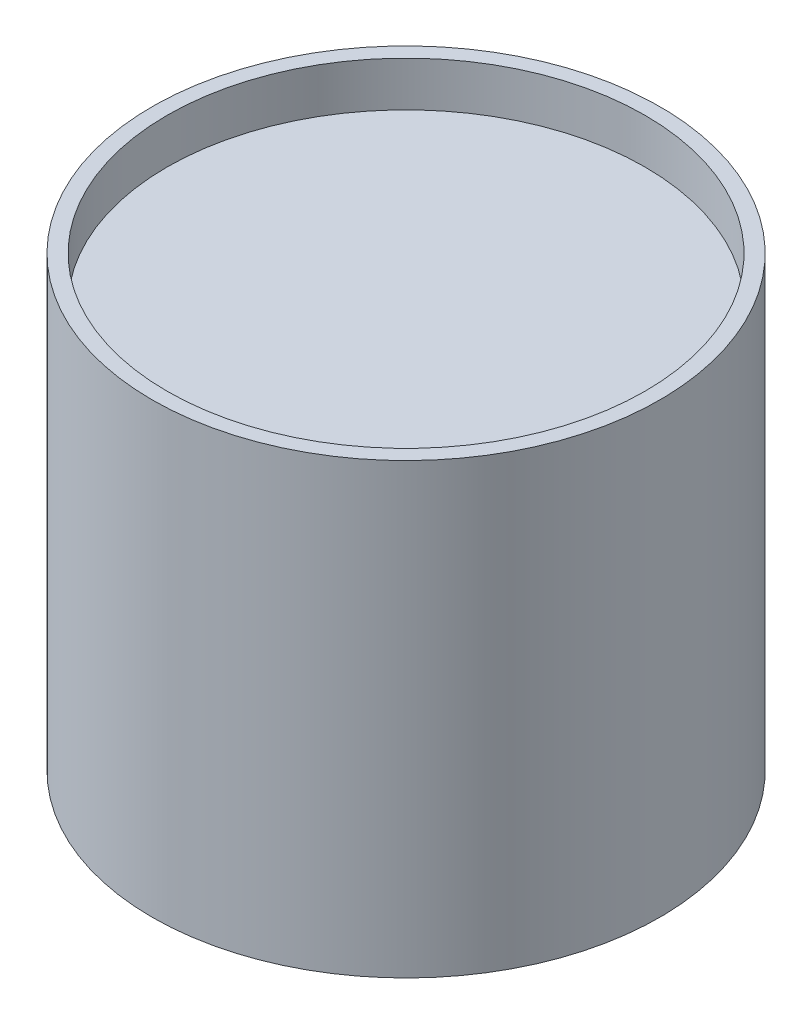
SolidWorks part; units mm, degrees
ref_plane "Front Plane" through (0, 0, 0) normal (0, 0, 1) x (1, 0, 0)
ref_plane "Top Plane" through (0, 0, 0) normal (0, 1, 0) x (1, 0, 0)
ref_plane "Right Plane" through (0, 0, 0) normal (1, 0, 0) x (0, 0, -1)
sketch "Sketch1" plane through (0, 0, 0) normal (0, 1, 0) x (1, 0, 0)
  circle A0 centre (0, 0) radius 17
  dimension "D1" = 34
extrude "Boss-Extrude1" add sketch "Sketch1" along normal blind 30
sketch "Sketch2" plane through (0, 30, 0) normal (0, 1, 0) x (1, 0, 0)
  circle A0 centre (0, 0) radius 16
  dimension "D1" = 32
extrude "Cut-Extrude1" cut sketch "Sketch2" against normal blind 3
sketch "Sketch3" plane through (0, 0, 0) normal (0, -1, 0) x (1, 0, 0)
  circle A0 centre (0, 0) radius 1
  dimension "D1" = 2
extrude "Cut-Extrude2" cut sketch "Sketch3" against normal blind 2
fillet "Fillet1" radius 1 1 edges at (0, 2, -1)
